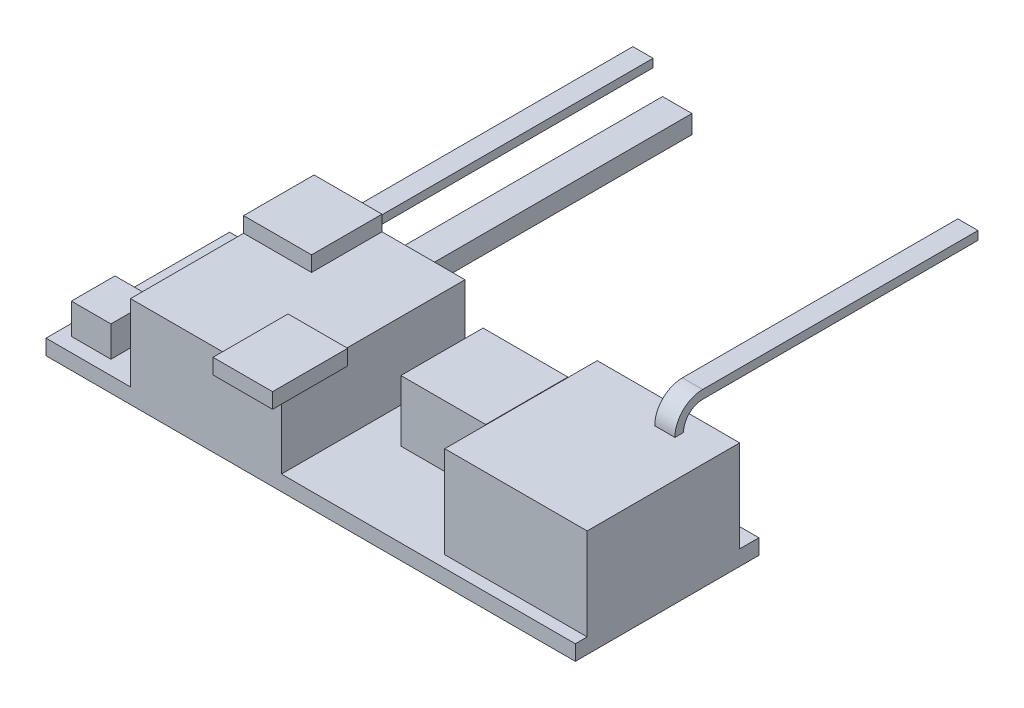
SolidWorks part; units mm, degrees
ref_plane "Front Plane" through (0, 0, 0) normal (0, 0, 1) x (1, 0, 0)
ref_plane "Top Plane" through (0, 0, 0) normal (0, 1, 0) x (1, 0, 0)
ref_plane "Right Plane" through (0, 0, 0) normal (1, 0, 0) x (0, 0, -1)
sketch "Sketch1" plane through (0, 0, 0) normal (0, 1, 0) x (1, 0, 0)
  line L1 (-79.6376, -24.4069) -> (140.0724, -24.4069)
  line L2 (-79.6376, -24.4069) -> (-79.6376, 51.7931)
  line L3 (-79.6376, 51.7931) -> (140.0724, 51.7931)
  line L4 (140.0724, -24.4069) -> (140.0724, 51.7931)
  dimension "D1" = 76.2
  dimension "D2" = 219.71
extrude "Boss-Extrude1" add sketch "Sketch1" along normal blind 6.35
sketch "Sketch2" plane through (0, 6.35, 0) normal (0, 1, 0) x (1, 0, 0)
  line L1 (-74.9908, -0.4303) -> (-58.5713, -0.4303)
  line L2 (-74.9908, -0.4303) -> (-74.9908, -18.5204)
  line L3 (-74.9908, -18.5204) -> (-58.5713, -18.5204)
  line L4 (-58.5713, -0.4303) -> (-58.5713, -18.5204)
extrude "Boss-Extrude2" add sketch "Sketch2" along normal blind 12.7
sketch "Sketch3" plane through (0, 6.35, 0) normal (0, 1, 0) x (1, 0, 0)
  line L0 (140.0724, 51.7931) -> (-79.6376, 51.7931) construction
  line L1 (-44.5679, 51.7931) -> (18.0811, 51.7931)
  line L2 (-44.5679, 51.7931) -> (-44.5679, -24.4069)
  line L3 (-44.5679, -24.4069) -> (18.0811, -24.4069)
  line L4 (18.0811, 51.7931) -> (18.0811, -24.4069)
  line L5 (-79.6376, -24.4069) -> (140.0724, -24.4069) construction
extrude "Boss-Extrude3" add sketch "Sketch3" along normal blind 31.75
sketch "Sketch4" plane through (0, 38.1, 0) normal (0, 1, 0) x (1, 0, 0)
  line L1 (-44.5679, 51.7931) -> (-16.3694, 51.7931)
  line L2 (-44.5679, 51.7931) -> (-44.5679, 22.5476)
  line L3 (-44.5679, 22.5476) -> (-16.3694, 22.5476)
  line L4 (-16.3694, 51.7931) -> (-16.3694, 22.5476)
  line L5 (0, -3.5658) -> (24.7229, -3.5658)
  line L6 (0, -3.5658) -> (0, -34.7266)
  line L7 (0, -34.7266) -> (24.7229, -34.7266)
  line L8 (24.7229, -3.5658) -> (24.7229, -34.7266)
extrude "Boss-Extrude4" add sketch "Sketch4" along normal blind 6.35
sketch "Sketch5" plane through (0, 6.35, 0) normal (0, 1, 0) x (1, 0, 0)
  line L1 (32.8512, 44.5279) -> (68.0692, 44.5279)
  line L2 (32.8512, 44.5279) -> (32.8512, 10.409)
  line L3 (32.8512, 10.409) -> (68.0692, 10.409)
  line L4 (68.0692, 44.5279) -> (68.0692, 10.409)
extrude "Boss-Extrude5" add sketch "Sketch5" along normal blind 25.4
sketch "Sketch6" plane through (0, 6.35, 0) normal (0, 1, 0) x (1, 0, 0)
  line L0 (140.0724, -24.4069) -> (140.0724, 51.7931) construction
  line L1 (80.9596, 43.8142) -> (140.0724, 43.8142)
  line L2 (80.9596, 43.8142) -> (80.9596, -19.5)
  line L3 (80.9596, -19.5) -> (140.0724, -19.5)
  line L4 (140.0724, 43.8142) -> (140.0724, -19.5)
extrude "Boss-Extrude6" add sketch "Sketch6" along normal blind 38.1
sketch "Sketch7" plane through (0, 44.45, 0) normal (0, 1, 0) x (1, 0, 0)
  line L1 (124.6946, 35.8683) -> (116.3126, 35.8683)
  line L2 (124.6946, 35.8683) -> (124.6946, 32.3123)
  line L3 (124.6946, 32.3123) -> (116.3126, 32.3123)
  line L4 (116.3126, 35.8683) -> (116.3126, 32.3123)
  dimension "D1" = 3.556
  dimension "D2" = 8.382
revolve "Revolve1" add sketch "Sketch7" angle 90 about axis through (80.9596, 44.45, -43.8142) along (-1, 0, 0)
sketch "Sketch8" plane through (0, 0, -43.8142) normal (0, 0, -1) x (-1, 0, 0)
  line L1 (-124.6946, 52.3959) -> (-116.3126, 52.3959)
  line L2 (-124.6946, 52.3959) -> (-124.6946, 55.9519)
  line L3 (-124.6946, 55.9519) -> (-116.3126, 55.9519)
  line L4 (-116.3126, 52.3959) -> (-116.3126, 55.9519)
extrude "Boss-Extrude7" add sketch "Sketch8" along normal blind 114.3
sketch "Sketch9" plane through (0, 0, -51.7931) normal (0, 0, -1) x (-1, 0, 0)
  line L0 (26.531, 40.7338) -> (-140.4506, 40.7338) construction
  line L1 (18.149, 42.4483) -> (26.531, 42.4483)
  line L2 (18.149, 42.4483) -> (18.149, 39.0193)
  line L3 (18.149, 39.0193) -> (26.531, 39.0193)
  line L4 (26.531, 42.4483) -> (26.531, 39.0193)
  dimension "D1" = 8.382
  dimension "D2" = 3.429
extrude "Boss-Extrude8" add sketch "Sketch9" along normal blind 114.3
sketch "Sketch10" plane through (0, 0, -51.7931) normal (0, 0, -1) x (-1, 0, 0)
  line L1 (14.2208, 30.6591) -> (2.018, 30.6591)
  line L2 (14.2208, 30.6591) -> (14.2208, 23.0391)
  line L3 (14.2208, 23.0391) -> (2.018, 23.0391)
  line L4 (2.018, 30.6591) -> (2.018, 23.0391)
  dimension "D1" = 7.62
  dimension "D2" = 12.2028
extrude "Boss-Extrude9" add sketch "Sketch10" along normal blind 114.3
equation "\"Deans Width\"= 0.14"
equation "\"D1@Sketch7\"=\"Deans Width\""
equation "\"Deans Length\"= .33"
equation "\"D2@Sketch7\"=\"Deans Length\""
